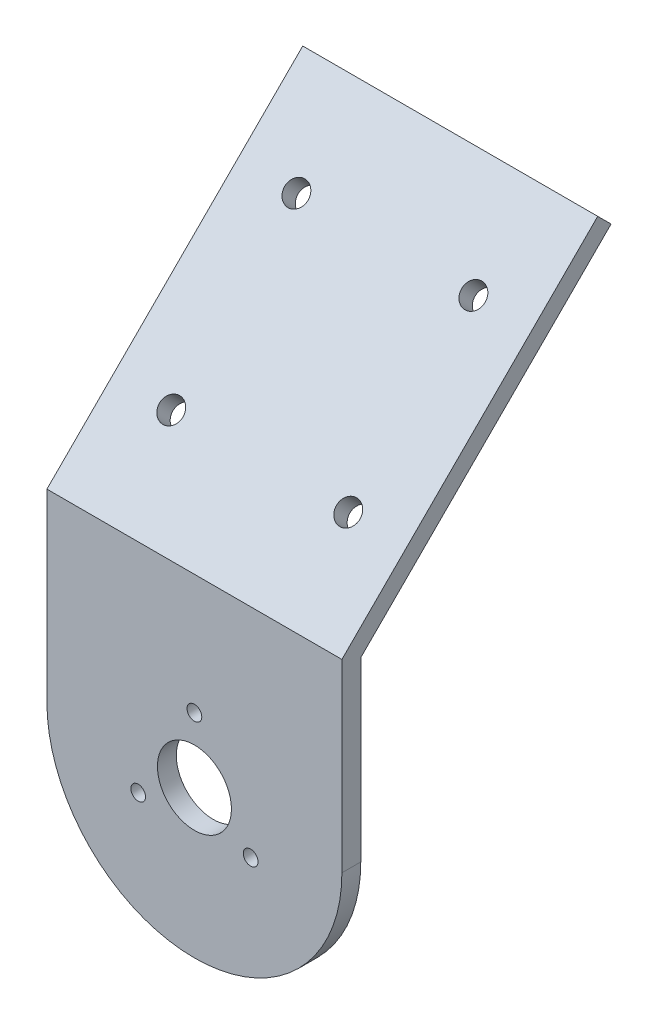
SolidWorks part; units mm, degrees
material "7075-T6 (SN)"
ref_plane "Front Plane" through (0, 0, 0) normal (0, 0, 1) x (1, 0, 0)
ref_plane "Top Plane" through (0, 0, 0) normal (0, 1, 0) x (1, 0, 0)
ref_plane "Right Plane" through (0, 0, 0) normal (1, 0, 0) x (0, 0, -1)
sketch "Sketch1" plane through (0, 0, 0) normal (0, 0, 1) x (1, 0, 0)
  line L0 (-25, 0) -> (-25, 30)
  line L1 (-25, 30) -> (25, 30)
  line L2 (25, 30) -> (25, 0)
  circle A0 centre (0, 0) radius 6.2732
  arc A1 (-25, 0) -> (25, 0) centre (0, 0) ccw
  circle A2 centre (0, 11) radius 1.25
  circle A3 centre (9.5263, -5.5) radius 1.25
  circle A4 centre (-9.5263, -5.5) radius 1.25
  dimension "D1" = 50
  dimension "D2" = 30
extrude "Boss-Extrude1" add sketch "Sketch1" along normal up to surface (3.2 mm away)
sketch "Sketch2" plane through (25, 0, 0) normal (1, 0, 0) x (0, 0, -1)
  line L0 (0, 30) -> (42.4264, 72.4264)
  line L1 (42.4264, 72.4264) -> (40.1637, 74.6891)
  line L2 (40.1637, 74.6891) -> (-3.2, 31.3255)
  line L3 (-3.2, 31.3255) -> (-3.2, 30)
  line L4 (-3.2, 30) -> (0, 30)
  line L5 (0, 0) -> (0, 30) construction
  dimension "D1" = 3.2
  dimension "D2" = 60
  dimension "D3" = 135
extrude "Boss-Extrude2" add sketch "Sketch2" against normal up to surface (50 mm away) up to face at (-25, 15, 1.6)
sketch "Sketch3" plane through (0, 17.2627, 17.2627) normal (0, 0.7071, 0.7071) x (1, 0, 0)
  line L0 (-25, 81.2132) -> (25, 81.2132) construction
  line L1 (-15, 35.5505) -> (15, 35.5505) construction
  line L2 (-15, 35.5505) -> (-15, 65.5505) construction
  line L3 (-15, 65.5505) -> (15, 65.5505) construction
  line L4 (15, 35.5505) -> (15, 65.5505) construction
  line L5 (-15, 35.5505) -> (15, 65.5505) construction
  line L6 (-15, 65.5505) -> (15, 35.5505) construction
  line L7 (-25, 19.8877) -> (-25, 81.2132) construction
  circle A0 centre (15, 65.5505) radius 2
  circle A1 centre (15, 35.5505) radius 2
  circle A2 centre (-15, 65.5505) radius 2
  circle A3 centre (-15, 35.5505) radius 2
  point P0 (0, 50.5505)
  point P8 (0, 81.2132)
  point P12 (-25, 50.5505)
  dimension "D3" = 4
  dimension "D4" = 4
  dimension "D5" = 4
  dimension "D6" = 4
  dimension "D1" = 30
  dimension "D2" = 30
extrude "Cut-Extrude1" cut sketch "Sketch3" against normal up to next
